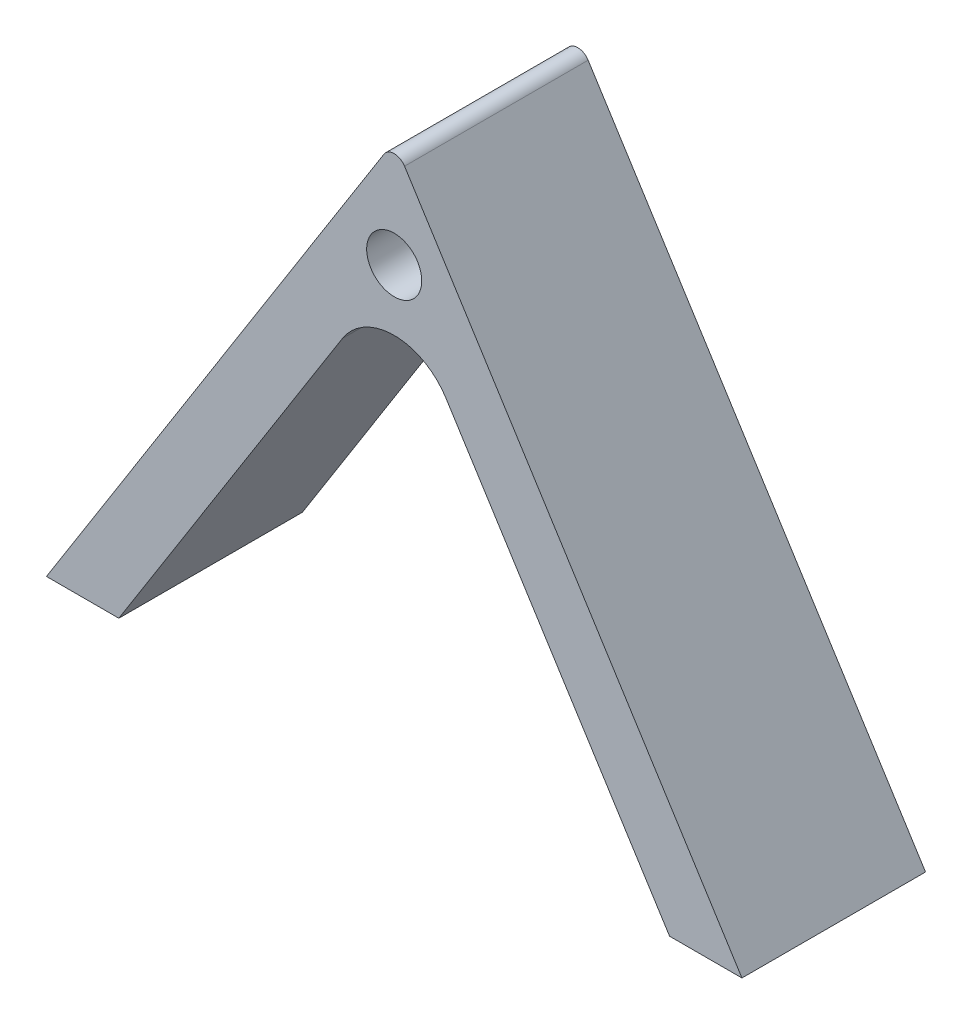
SolidWorks part; units mm, degrees
ref_plane "Front Plane" through (0, 0, 0) normal (0, 0, 1) x (1, 0, 0)
ref_plane "Top Plane" through (0, 0, 0) normal (0, 1, 0) x (1, 0, 0)
ref_plane "Right Plane" through (0, 0, 0) normal (1, 0, 0) x (0, 0, -1)
sketch "Sketch1" plane through (0, 0, 0) normal (0, 0, 1) x (1, 0, 0)
  line L0 (-56.8266, 0) -> (0, 90)
  line L1 (0, 90) -> (56.8266, 0)
  line L2 (56.8266, 0) -> (45, 0)
  line L3 (45, 0) -> (0, 71.2695)
  line L4 (0, 71.2695) -> (-45, 0)
  line L5 (-45, 0) -> (-56.8266, 0)
  point P6 (0, 0)
  point P8 (42.5418, 0)
  point P9 (-10.657, 70.7358)
  point P10 (0, 0)
  point P11 (-7.8558, 70.9803)
  dimension "D1" = 90
  dimension "D2" = 10
  dimension "D3" = 10
  dimension "D4" = 90
extrude "Boss-Extrude1" add sketch "Sketch1" along normal blind 30
fillet "Fillet1" radius 2 1 edges at (0, 90, 15)
fillet "Fillet2" radius 10 1 edges at (0, 71.2695, 15)
sketch "Sketch2" plane through (0, 0, 30) normal (0, 0, 1) x (1, 0, 0)
  circle A0 centre (0, 72.5) radius 4.5
  point P2 (0, 72.8336)
  dimension "D2" = 9
  dimension "D1" = 72.5
extrude "Cut-Extrude1" cut sketch "Sketch2" against normal through all
